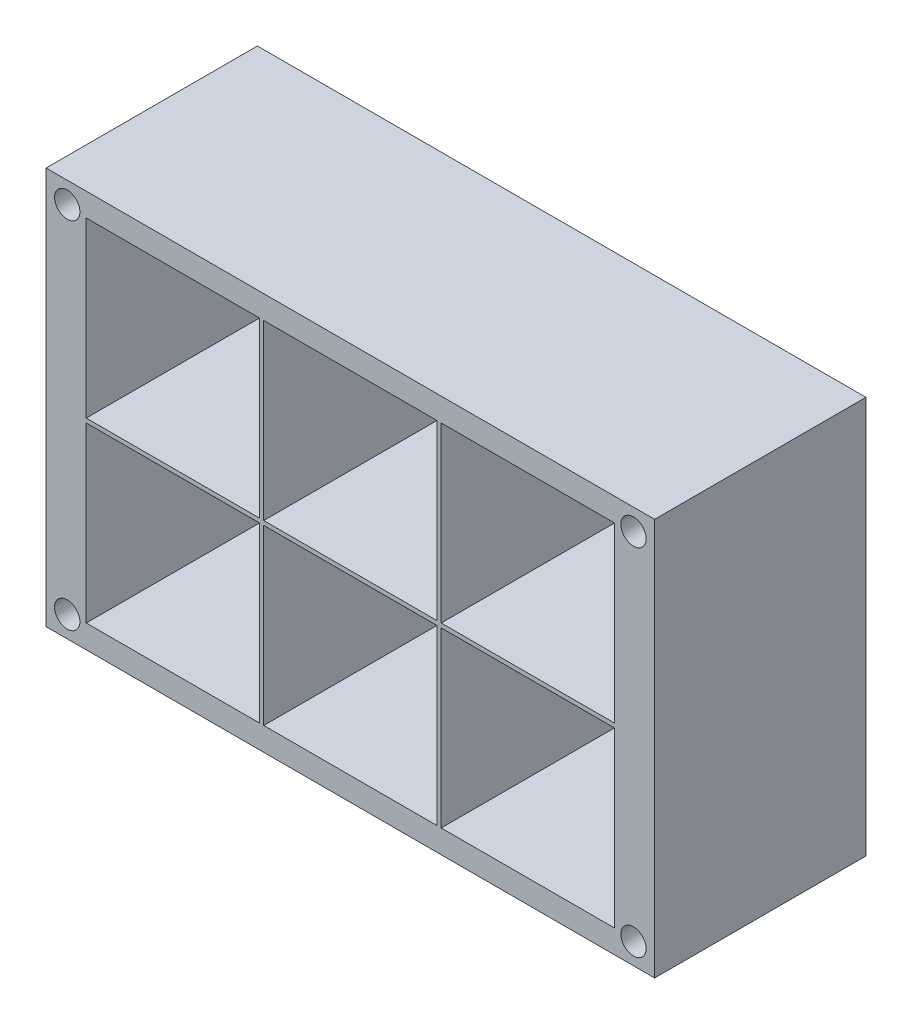
SolidWorks part; units mm, degrees
ref_plane "正面" through (0, 0, 0) normal (0, 0, 1) x (1, 0, 0)
ref_plane "平面" through (0, 0, 0) normal (0, 1, 0) x (1, 0, 0)
ref_plane "右側面" through (0, 0, 0) normal (1, 0, 0) x (0, 0, -1)
sketch "ｽｹｯﾁ1" plane through (0, 0, 0) normal (0, 0, 1) x (1, 0, 0)
  line L0 (-59.6348, 40.924) -> (-59.6348, 20.424)
  line L1 (-80.6348, 40.924) -> (-60.1348, 40.924)
  line L2 (-80.6348, 40.924) -> (-80.6348, 20.424)
  line L3 (-80.6348, 20.424) -> (-60.1348, 20.424)
  line L4 (-60.1348, 40.924) -> (-60.1348, 20.424)
  line L5 (-59.6348, 40.924) -> (-39.1348, 40.924)
  line L6 (-39.1348, 40.924) -> (-39.1348, 20.424)
  line L7 (-59.6348, 20.424) -> (-39.1348, 20.424)
  line L8 (-38.6348, 40.924) -> (-38.6348, 20.424)
  line L9 (-38.6348, 40.924) -> (-18.1348, 40.924)
  line L10 (-18.1348, 40.924) -> (-18.1348, 20.424)
  line L11 (-38.6348, 20.424) -> (-18.1348, 20.424)
  line L12 (-59.6348, 61.924) -> (-59.6348, 41.424)
  line L13 (-59.6348, 41.424) -> (-39.1348, 41.424)
  line L14 (-39.1348, 61.924) -> (-39.1348, 41.424)
  line L15 (-59.6348, 61.924) -> (-39.1348, 61.924)
  line L16 (-38.6348, 61.924) -> (-38.6348, 41.424)
  line L17 (-38.6348, 41.424) -> (-18.1348, 41.424)
  line L18 (-18.1348, 61.924) -> (-18.1348, 41.424)
  line L19 (-38.6348, 61.924) -> (-18.1348, 61.924)
  line L20 (-80.6348, 61.924) -> (-80.6348, 41.424)
  line L21 (-80.6348, 61.924) -> (-60.1348, 61.924)
  line L22 (-60.1348, 61.924) -> (-60.1348, 41.424)
  line L23 (-80.6348, 41.424) -> (-60.1348, 41.424)
  line L25 (-85.3848, 64.674) -> (-13.3848, 64.674)
  line L26 (-85.3848, 64.674) -> (-85.3848, 17.674)
  line L27 (-85.3848, 17.674) -> (-13.3848, 17.674)
  line L28 (-13.3848, 64.674) -> (-13.3848, 17.674)
  dimension "D1" = 20.5
  dimension "D2" = 20.5
  dimension "D5" = 0.5
  dimension "D6" = 2.75
  dimension "D7" = 4.75
  dimension "D8" = 2.75
  dimension "D9" = 0.5
  dimension "D10" = 4.75
  dimension "D3" = 3
  dimension "D4" = 2
extrude "ﾎﾞｽ - 押し出し1" add sketch "ｽｹｯﾁ1" along normal blind 25
sketch "ｽｹｯﾁ2" plane through (0, 0, 25) normal (0, 0, 1) x (1, 0, 0)
  line L0 (-13.3848, 64.674) -> (-85.3848, 64.674) construction
  line L1 (-13.3848, 17.674) -> (-13.3848, 64.674) construction
  circle A0 centre (-15.8848, 62.174) radius 1.5
  circle A1 centre (-82.8848, 62.174) radius 1.5
  circle A2 centre (-82.8848, 20.174) radius 1.5
  circle A3 centre (-15.8848, 20.174) radius 1.5
  dimension "D1" = 3
  dimension "D2" = 2.5
  dimension "D3" = 2.5
  dimension "D4" = 2
  dimension "D5" = 2
extrude "ｶｯﾄ - 押し出し1" cut sketch "ｽｹｯﾁ2" against normal through all
